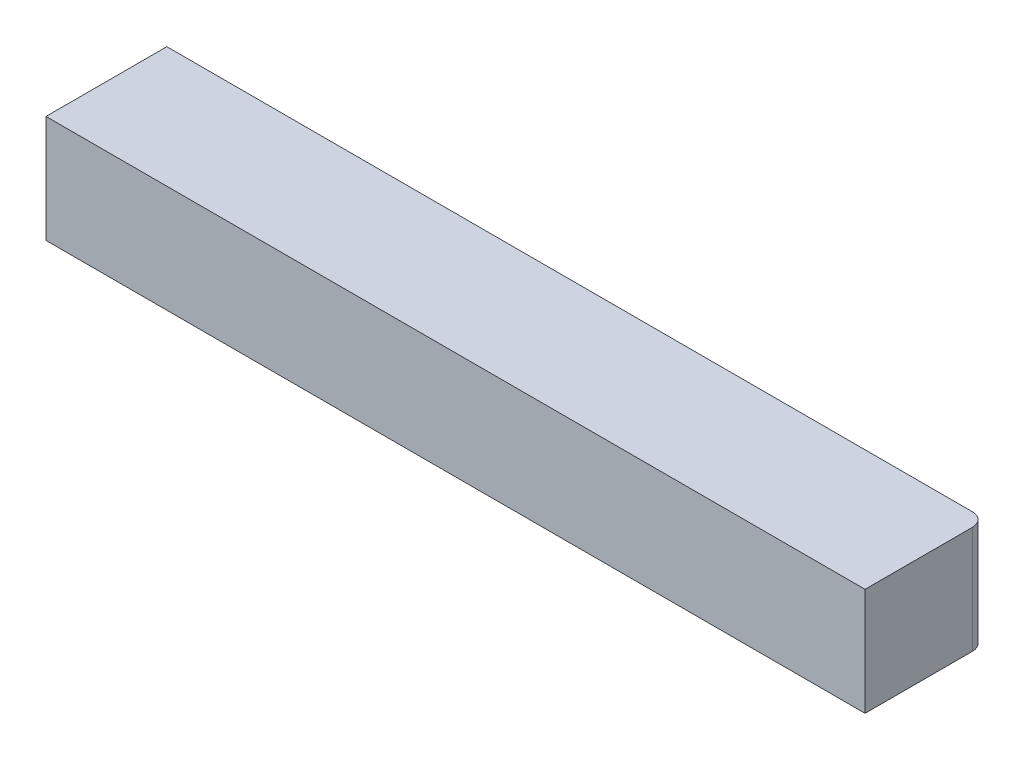
SolidWorks part; units mm, degrees
material "Air"
ref_plane "Front Plane" through (0, 0, 0) normal (0, 0, 1) x (1, 0, 0)
ref_plane "Top Plane" through (0, 0, 0) normal (0, 1, 0) x (1, 0, 0)
ref_plane "Right Plane" through (0, 0, 0) normal (1, 0, 0) x (0, 0, -1)
sketch "Sketch1" plane through (0, 0, 0) normal (0, 1, 0) x (1, 0, 0)
  line L0 (-30.5, 4.5) -> (30.5, -4.5) construction
  line L1 (-30.5, -4.5) -> (30.5, -4.5)
  line L2 (-30.5, -4.5) -> (-30.5, 4.5)
  line L3 (-30.5, 4.5) -> (29.5, 4.5)
  line L4 (30.5, -4.5) -> (30.5, 3.5)
  line L5 (30.5, 3.5) -> (30.5, 4.5) construction
  line L6 (30.5, 4.5) -> (29.5, 4.5) construction
  arc A0 (29.5, 4.5) -> (30.5, 3.5) centre (29.5, 3.5) cw
  point P4 (29.5, 4.5)
  point P5 (30.5, 3.5)
  dimension "D3" = 1
  dimension "D4" = 1
  dimension "D1" = 9
  dimension "D2" = 61
  dimension "D5" = 1
extrude "Boss-Extrude1" add sketch "Sketch1" along normal blind 8
